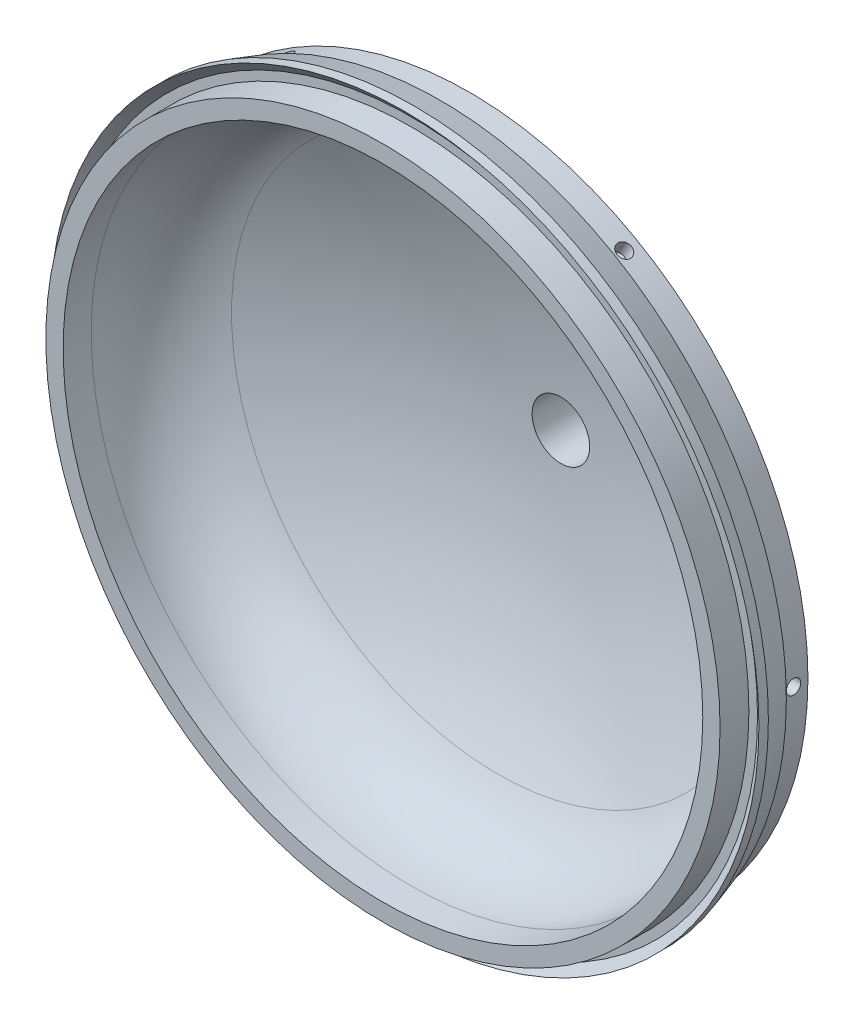
SolidWorks part; units mm, degrees
material "6061-T6 (SS)"
ref_plane "Front Plane" through (0, 0, 0) normal (0, 0, 1) x (1, 0, 0)
ref_plane "Top Plane" through (0, 0, 0) normal (0, 1, 0) x (1, 0, 0)
ref_plane "Right Plane" through (0, 0, 0) normal (1, 0, 0) x (0, 0, -1)
sketch "Sketch1" plane through (0, 0, 0) normal (0, 1, 0) x (1, 0, 0)
  line L0 (0, 0) -> (-140.97, 0) construction
  line L1 (-140.97, 0) -> (-148.59, 0)
  line L2 (-148.59, 0) -> (-148.59, 12.7)
  line L7 (0, 0) -> (0, 12.391) construction
  line L8 (0, 78.7237) -> (0, 85.0737)
  line L9 (-140.97, 0) -> (-140.97, 12.391)
  line L10 (98.044, 12.391) -> (-98.044, 12.391) construction
  line L29 (-152.4, 12.7) -> (-152.4, 9.503) construction
  line L30 (-152.4, 9.503) -> (-156.21, 9.503) construction
  line L31 (-152.4, 25.4) -> (-156.21, 13.674)
  line L32 (-152.4, 12.7) -> (-156.21, 9.503)
  line L33 (-152.4, 25.4) -> (-156.21, 25.4) construction
  line L34 (-156.21, 13.674) -> (-156.21, 25.4) construction
  line L35 (-152.4, 25.4) -> (-149.225, 25.4)
  line L36 (-152.4, 12.7) -> (-152.4, 25.4) construction
  line L37 (-149.225, 25.4) -> (-149.225, 38.1)
  line L38 (-149.225, 38.1) -> (-140.0818, 38.1)
  line L39 (-152.4, 12.7) -> (-148.59, 12.7)
  line L40 (-156.21, 13.674) -> (-156.21, 9.503)
  line L41 (0, 0) -> (0, 85.725) construction
  arc A7 (-115.4202, 51.6429) -> (-140.97, 12.391) centre (-98.044, 12.391) ccw
  arc A9 (-120.3033, 56.353) -> (-140.0818, 38.1) centre (-98.044, 12.391) ccw
  circle A11 centre (-98.044, 12.391) radius 217.043 construction
  circle A14 centre (98.044, 12.391) radius 217.043 construction
  arc A15 (0, 78.7237) -> (-117.4348, 50.6878) centre (0, -181.2453) ccw
  arc A16 (0, 85.0737) -> (-120.3033, 56.353) centre (0, -181.2453) ccw
  point P19 (0, 12.391)
  dimension "D19" = 42.926
  dimension "D20" = 259.969
  dimension "D21" = 266.319
  dimension "D22" = 266.319
  dimension "D11" = 12.391
  dimension "D13" = 434.086
  dimension "D14" = 434.086
  dimension "D16" = 49.276
  dimension "D2" = 3.81
  dimension "D3" = 7.62
  dimension "D4" = 12.7
  dimension "D5" = 3.81
  dimension "D6" = 3.81
  dimension "D7" = 18
  dimension "D8" = 85.725
  dimension "D9" = 50
  dimension "D10" = 152.4
  dimension "D12" = 3.175
  dimension "D15" = 12.7
  dimension "D17" = 25.4
  dimension "D18" = 196.088
ref_axis "Axis1" through (0, 0, 5.4731) along (0, 0, -1)
revolve "Revolve1" add sketch "Sketch1" angle 360 about L8
ref_plane "Plane1" through (0, 0, -86.36) normal (0, 0, 1) x (1, 0, 0)
sketch "Sketch6" plane through (0, 0, -86.36) normal (0, 0, 1) x (1, 0, 0)
  circle A0 centre (76.2, 0) radius 25.4
  circle A2 centre (-76.2, 0) radius 21.515
  dimension "D1" = 152.4
  dimension "D2" = 43.03
  dimension "D3" = 50.8
  dimension "D4" = 76.2
ref_plane "Plane3" through (0, 0, -101.6) normal (0, 0, 1) x (1, 0, 0)
ref_plane "Plane4" through (0, 0, -96.52) normal (0, 0, 1) x (1, 0, 0)
sketch "Sketch10" plane through (0, 0, -96.52) normal (0, 0, 1) x (1, 0, 0)
  circle A0 centre (0, 0) radius 25.4
  dimension "D1" = 50.8
extrude "Boss-Extrude2" add sketch "Sketch10" along normal up to surface (19.0401 mm away)
sketch "Sketch11" plane through (0, 0, 0) normal (0, 0, 1) x (1, 0, 0)
  circle A0 centre (0, 0) radius 12.7
  dimension "D1" = 25.4
extrude "Cut-Extrude1" cut sketch "Sketch11" against normal blind 190.754 contours A0
ref_plane "Plane5" through (149.225, 0, 0) normal (1, 0, 0) x (0, 0, -1)
sketch "Sketch13" plane through (149.225, 0, 0) normal (1, 0, 0) x (0, 0, -1)
  line L0 (25.4, 0) -> (38.1, 0) construction
  line L1 (25.4, -149.225) -> (25.4, 149.225) construction
  line L2 (38.1, -140.0818) -> (38.1, 140.0818) construction
  circle A0 centre (31.75, 0) radius 3.175
  point P10 (31.75, 0)
  dimension "D1" = 6.35
hole_wizard "1/4 (0.25) Diameter Hole1" positions "Sketch14" profile "Sketch15" hole size "1/4" standard "ANSI Inch"
sketch "Sketch14" plane through (149.225, 0, 0) normal (1, 0, 0) x (0, 0, -1)
  point P0 (31.75, 0)
sketch "Sketch15" plane through (149.225, 0, -31.75) normal (0, 1, 0) x (0, 0, -1)
  line L0 (0, 0) -> (0, 8.2577)
  line L1 (0, 8.2577) -> (3.175, 6.35)
  line L2 (3.175, 6.35) -> (3.175, 0)
  line L5 (3.175, 0) -> (0, 0)
  line L10 (0, 8.2577) -> (-3.175, 6.35) construction
  line L11 (0, -6.35) -> (0, 107.95) construction
  dimension "Hole Dia." = 6.35
  dimension "Hole Depth" = 6.35
  dimension "Drill Angle" = 118
pattern_circular "CirPattern1" count 6 over 360 about axis through (0, 0, 5.4731) along (0, 0, -1) of "1/4 (0.25) Diameter Hole1"
